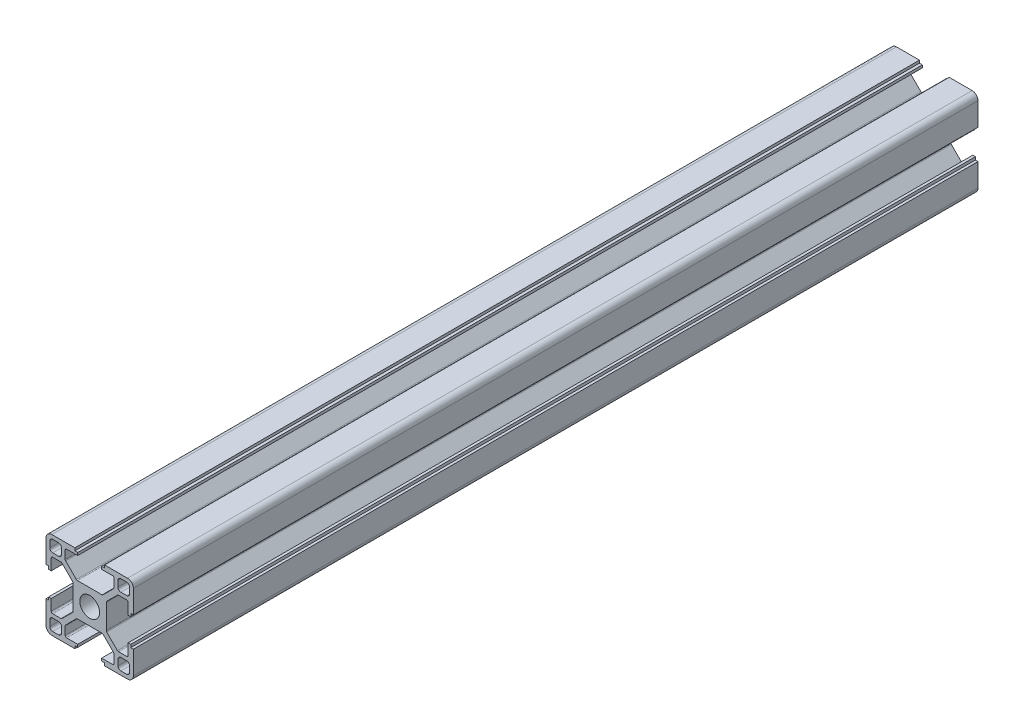
SolidWorks part; units mm, degrees
ref_plane "前视基准面" through (0, 0, 0) normal (0, 0, 1) x (1, 0, 0)
ref_plane "上视基准面" through (0, 0, 0) normal (0, 1, 0) x (1, 0, 0)
ref_plane "右视基准面" through (0, 0, 0) normal (1, 0, 0) x (0, 0, -1)
sketch "草图1" plane through (0, 0, 0) normal (0, 0, 1) x (1, 0, 0)
  line L0 (0, 0) -> (0, 65.3905) construction
  line L1 (0, 0) -> (64.2648, 0) construction
  line L2 (0, 0) -> (79.9729, 79.9729) construction
  line L3 (5.7, 0) -> (5.7, 4.4272)
  line L4 (5.7, 4.4272) -> (9.6728, 8.4)
  line L5 (9.6728, 8.4) -> (13.2, 8.4)
  line L6 (13.2, 8.4) -> (13.2, 4.1)
  line L7 (13.2, 4.1) -> (14.1, 4.1)
  line L8 (14.1, 4.1) -> (14.1, 5.1)
  line L9 (14.1, 5.1) -> (15, 5.1)
  line L10 (15, 5.1) -> (15, 15)
  line L11 (5.1, 15) -> (15, 15)
  line L12 (5.1, 14.1) -> (5.1, 15)
  line L13 (4.1, 14.1) -> (5.1, 14.1)
  line L14 (4.1, 13.2) -> (4.1, 14.1)
  line L15 (8.4, 13.2) -> (4.1, 13.2)
  line L16 (8.4, 9.6728) -> (8.4, 13.2)
  line L17 (4.4272, 5.7) -> (8.4, 9.6728)
  line L18 (0, 5.7) -> (4.4272, 5.7)
  line L20 (9.7, 9.7) -> (13.7, 9.7)
  line L21 (9.7, 9.7) -> (9.7, 13.7)
  line L22 (9.7, 13.7) -> (13.7, 13.7)
  line L23 (13.7, 9.7) -> (13.7, 13.7)
  line L24 (9.7, 9.7) -> (13.7, 13.7) construction
  line L25 (9.7, 13.7) -> (13.7, 9.7) construction
  line L26 (0, 5.7) -> (0, 0)
  line L27 (0, 0) -> (5.7, 0)
  point P9 (11.7, 11.7)
  dimension "D1" = 45
  dimension "D2" = 5.7
  dimension "D3" = 1.8
  dimension "D4" = 0.9
  dimension "D5" = 8.2
  dimension "D6" = 10.2
  dimension "D7" = 1.8
  dimension "D8" = 15
  dimension "D9" = 16.8
  dimension "D10" = 4
  dimension "D11" = 1.3
extrude "凸台-拉伸1" add sketch "草图1" along normal blind 290 contours L3 L4 L5 L6 L7 L8 L9 L10 L11 L12 L13 L14 L15 L16 L17 L18 L26 L27
fillet "圆角1" radius 1 4 edges at (9.7, 9.7, 145) (13.7, 9.7, 145) (9.7, 13.7, 145) (13.7, 13.7, 145)
fillet "圆角2" radius 2 1 edges at (15, 15, 145)
fillet "圆角3" radius 0.5 6 edges at (5.7, 4.4272, 145) (4.4272, 5.7, 145) (8.4, 13.2, 145) (8.4, 9.6728, 145) (9.6728, 8.4, 145) (13.2, 8.4, 145)
pattern_circular "阵列(圆周)1" count 4 over 360 about axis through (0, 0, 0) along (0, 0, 1) of "圆角2", "圆角3", "凸台-拉伸1", "圆角1"
sketch "草图2" plane through (0, 0, 290) normal (0, 0, 1) x (1, 0, 0)
  circle A0 centre (0, 0) radius 3.4
  dimension "D1" = 6.8
extrude "切除-拉伸1" cut sketch "草图2" against normal through all
cosmetic thread "装饰螺纹线1" parameters "D1"=20, "D2"=8
cosmetic thread "装饰螺纹线2" parameters "D1"=20, "D2"=8
sketch "草图3" plane through (0, 0, 0) normal (1, 0, 0) x (0, 0, -1)
  line L0 (-145, 60.2652) -> (-145, -70.1349) construction
  line L1 (-318.169, 0) -> (51.4974, 0) construction
  line L2 (0, 5.1) -> (0, 13) construction
  line L3 (-290, 5.1) -> (-290, 13) construction
  circle A0 centre (-145, 0) radius 3.05
  dimension "D1" = 6.1
extrude "切除-拉伸2" cut sketch "草图3" against normal mid plane 20
